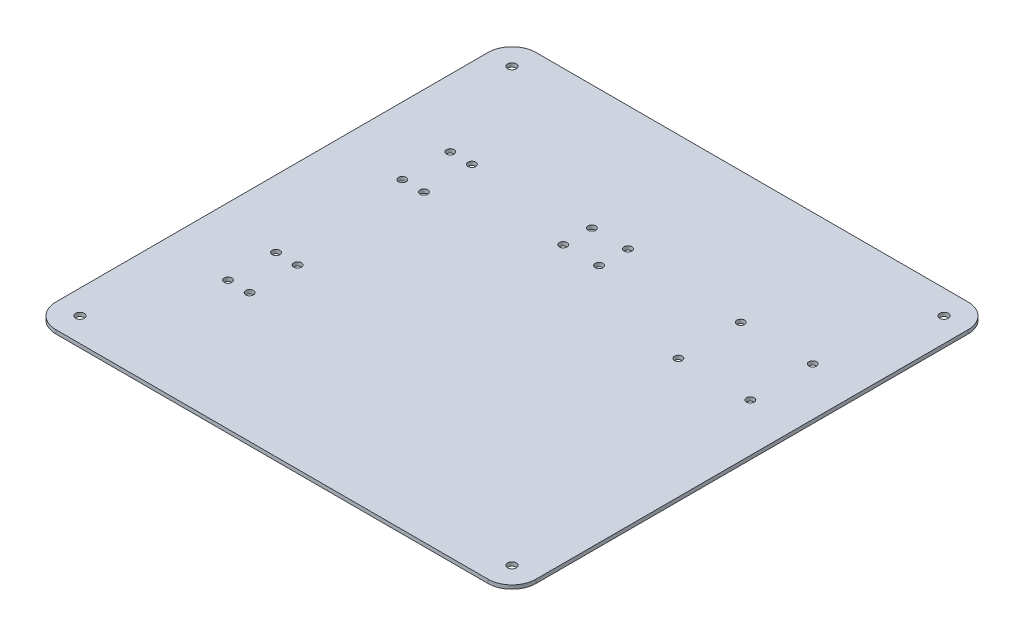
SolidWorks part; units mm, degrees
material "PTFE (general)"
ref_plane "Front Plane" through (0, 0, 0) normal (0, 0, 1) x (1, 0, 0)
ref_plane "Top Plane" through (0, 0, 0) normal (0, 1, 0) x (1, 0, 0)
ref_plane "Right Plane" through (0, 0, 0) normal (1, 0, 0) x (0, 0, -1)
sketch "Sketch2" plane through (0, 0, 0) normal (0, 1, 0) x (1, 0, 0)
  line L1 (-100, 100) -> (100, 100)
  line L2 (-100, 100) -> (-100, -100)
  line L3 (-100, -100) -> (100, -100)
  line L4 (100, 100) -> (100, -100)
  line L5 (-100, 100) -> (100, -100) construction
  line L6 (-100, -100) -> (100, 100) construction
  point P0 (0, 0)
extrude "Boss-Extrude1" add sketch "Sketch2" along normal blind 1.57
hole_wizard "Ø3.6 (3.6) Diameter Hole1" positions "Sketch3" profile "Sketch4" hole size "Ø3.6" standard "ANSI Metric"
sketch "Sketch3" plane through (0, 1.57, 0) normal (0, 1, 0) x (1, 0, 0)
  line L0 (100, 100) -> (-100, 100) construction
  line L1 (-100, 100) -> (-100, -100) construction
  line L2 (100, -100) -> (100, 100) construction
  line L3 (-100, -100) -> (100, -100) construction
  point P0 (-90, 90)
  point P2 (90, 90)
  point P4 (90, -90)
  point P6 (-90, -90)
  dimension "D1" = 10
  dimension "D2" = 10
  dimension "D3" = 10
  dimension "D4" = 10
  dimension "D5" = 10
  dimension "D6" = 10
  dimension "D7" = 10
  dimension "D8" = 10
sketch "Sketch4" plane through (-90, 1.57, -90) normal (1, 0, 0) x (0, 0, 1)
  line L0 (0, 0) -> (0, 4.2815)
  line L1 (0, 4.2815) -> (1.8, 3.2)
  line L2 (1.8, 3.2) -> (1.8, 0)
  line L5 (1.8, 0) -> (0, 0)
  line L10 (0, 4.2815) -> (-1.8, 3.2) construction
  line L11 (0, -6.35) -> (0, 107.95) construction
  dimension "Hole Dia." = 3.6
  dimension "Hole Depth" = 3.2
  dimension "Drill Angle" = 118
hole_wizard "Ø3.2 (3.2) Diameter Hole1" positions "Sketch6" profile "Sketch7" hole size "Ø3.2" standard "ANSI Metric"
sketch "Sketch6" plane through (0, 0, 0) normal (0, -1, 0) x (-1, 0, 0)
  point P0 (15, 48.3)
  point P3 (0, 48.3)
  point P6 (0, 36.3)
  point P9 (15, 36.3)
  point P12 (63, 46.3)
  point P15 (72, 46.3)
  point P18 (63, 26.3)
  point P21 (72, 26.3)
  point P24 (-50, 45.3)
  point P27 (-79.9837, 45.3)
  point P30 (-79.9837, 19.3)
  point P33 (-50, 19.3)
  point P38 (72, -26.3)
  point P40 (63, -26.3)
  point P42 (63, -46.3)
  point P44 (72, -46.3)
sketch "Sketch7" plane through (-15, 0, -48.3) normal (1, 0, 0) x (0, 0, -1)
  line L0 (0, 0) -> (0, 2.5314)
  line L1 (0, 2.5314) -> (1.6, 1.57)
  line L2 (1.6, 1.57) -> (1.6, 0)
  line L5 (1.6, 0) -> (0, 0)
  line L10 (0, 2.5314) -> (-1.6, 1.57) construction
  line L11 (0, -6.35) -> (0, 107.95) construction
  dimension "Hole Dia." = 3.2
  dimension "Hole Depth" = 1.57
  dimension "Drill Angle" = 118
sketch "Sketch8" plane through (0, 1.57, 0) normal (0, 1, 0) x (1, 0, 0)
  line L0 (100, -100) -> (100, 100) construction
  line L1 (1, -5) -> (55, -5)
  line L2 (1, -5) -> (1, -98)
  line L3 (1, -98) -> (55, -98)
  line L4 (55, -5) -> (55, -98)
  line L5 (1, -5) -> (55, -98) construction
  line L6 (1, -98) -> (55, -5) construction
  line L7 (-100, -100) -> (100, -100) construction
  point P0 (28, -51.5)
  dimension "D1" = 45
  dimension "D2" = 2
  dimension "D3" = 93
  dimension "D4" = 54
sketch "Sketch9" [suppressed] plane through (0, 1.57, 0) normal (0, 1, 0) x (1, 0, 0)
  line L0 (-80, 51.3) -> (-75, 56.3)
  line L1 (-75, 56.3) -> (-60, 56.3)
  line L2 (-60, 56.3) -> (-55, 51.3)
  line L3 (-55, 51.3) -> (-55, 13.0345)
  line L4 (-55, 13.0345) -> (-80, 13.3)
  line L5 (-80, 13.3) -> (-80, 51.3)
  line L6 (-51.1712, 75) -> (-51.1712, 90)
  line L7 (-51.1712, 90) -> (-31.1712, 90)
  line L8 (-31.1712, 90) -> (-31.1712, 75)
  line L9 (-31.1712, 75) -> (-51.1712, 75)
  line L10 (-45, 67) -> (-45, 46.68)
  line L11 (-45, 46.68) -> (-36.11, 46.68)
  line L12 (-36.11, 46.68) -> (-36.11, 67)
  line L13 (-36.11, 67) -> (-45, 67)
  line L14 (-25, 51.3) -> (-20, 56.3)
  line L15 (-20, 56.3) -> (5, 56.3)
  line L16 (5, 56.3) -> (10, 51.3)
  line L17 (10, 51.3) -> (9.9495, 25.3)
  line L18 (9.9495, 25.3) -> (-25, 25.3)
  line L19 (-25, 25.3) -> (-25, 51.3)
  line L20 (40, 51.3) -> (45, 56.3)
  line L21 (45, 56.3) -> (84.9837, 56.3)
  line L22 (84.9837, 56.3) -> (89.9837, 51.3)
  line L23 (89.9837, 51.3) -> (89.9837, 5.3)
  line L24 (89.9837, 5.3) -> (39.9837, 5.3)
  line L25 (39.9837, 5.3) -> (40, 51.3)
  line L26 (-80, -13.3) -> (-55, -13.3)
  line L27 (-55, -13.3) -> (-55, -51.3)
  line L28 (-55, -51.3) -> (-60, -56.3)
  line L29 (-60, -56.3) -> (-75, -56.3)
  line L30 (-75, -56.3) -> (-80, -51.3)
  line L31 (-80, -51.3) -> (-80, -13.3)
  line L32 (-45, -46.68) -> (-36.11, -46.68)
  line L33 (-36.11, -46.68) -> (-36.11, -67)
  line L34 (-36.11, -67) -> (-45, -67)
  line L35 (-45, -67) -> (-45, -46.68)
  line L36 (-52, -75) -> (-32, -75)
  line L37 (-32, -75) -> (-32, -90)
  line L38 (-32, -90) -> (-52, -90)
  line L39 (-52, -90) -> (-52, -75)
  line L40 (91, -22) -> (100, -22)
  line L41 (100, -100) -> (100, 100) construction
  line L42 (91, -22) -> (100, -22) construction
  line L43 (100, -22) -> (100, -80)
  line L44 (100, -80) -> (91, -80) construction
  line L45 (100, -80) -> (91, -80)
  line L46 (91, -80) -> (91, -22)
  line L48 (-12.58, 68.7) -> (-2.4191, 68.7)
  line L49 (-12.58, 68.7) -> (-12.58, 66.2936)
  line L50 (-12.58, 66.2936) -> (-2.4191, 66.2936)
  line L51 (-2.4191, 68.7) -> (-2.4191, 66.2936)
  line L52 (59.91, 68.7) -> (70.07, 68.7)
  line L53 (59.91, 68.7) -> (59.91, 66.3)
  line L54 (59.91, 66.3) -> (70.07, 66.3)
  line L55 (70.07, 68.7) -> (70.07, 66.3)
fillet "Fillet1" radius 10 1 edges at (100, 0.785, 100)
fillet "Fillet2" radius 10 3 edges at (100, 0.785, -100) (-100, 0.785, -100) (-100, 0.785, 100)
